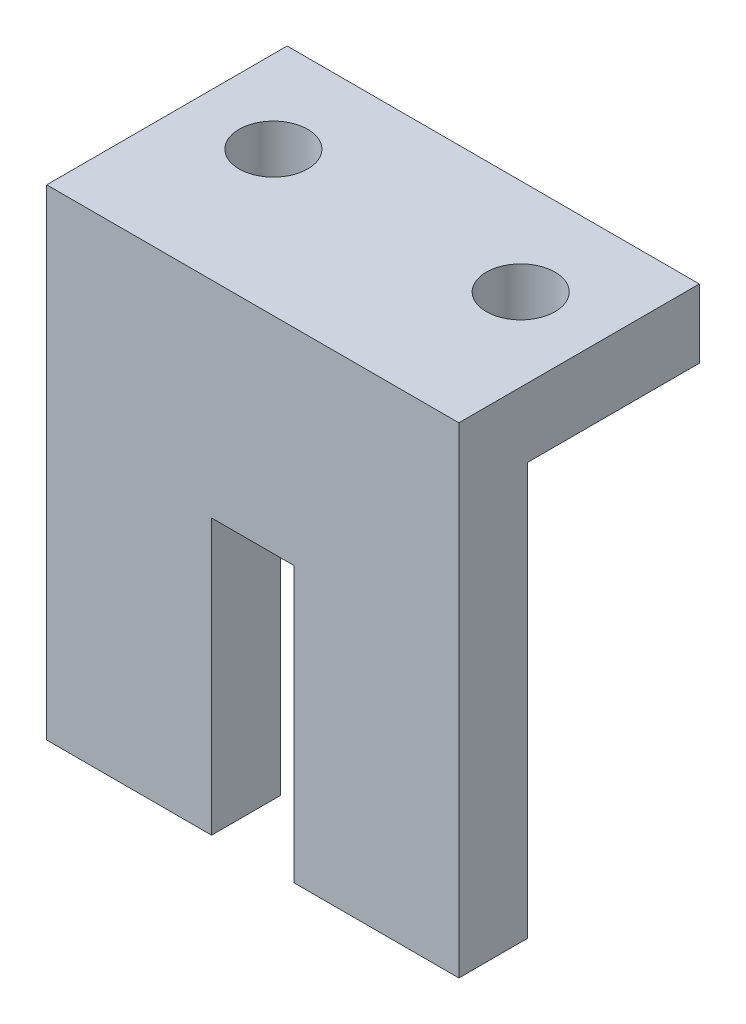
SolidWorks part; units mm, degrees
ref_plane "Front Plane" through (0, 0, 0) normal (0, 0, 1) x (1, 0, 0)
ref_plane "Top Plane" through (0, 0, 0) normal (0, 1, 0) x (1, 0, 0)
ref_plane "Right Plane" through (0, 0, 0) normal (1, 0, 0) x (0, 0, -1)
sketch "Sketch1" plane through (0, 0, 0) normal (0, 0, 1) x (1, 0, 0)
  line L0 (12, 0) -> (12, 20)
  line L1 (0, 0) -> (12, 0)
  line L2 (0, 0) -> (0, 30)
  line L4 (30, 0) -> (30, 30)
  line L5 (12, 20) -> (18, 20)
  line L6 (18, 20) -> (18, 0)
  line L7 (18, 0) -> (30, 0)
  line L8 (0, 30) -> (0, 35)
  line L9 (0, 35) -> (30, 35)
  line L10 (30, 35) -> (30, 30)
  dimension "D1" = 30
  dimension "D2" = 30
  dimension "D3" = 12
  dimension "D4" = 6
  dimension "D5" = 20
  dimension "D6" = 5
extrude "Boss-Extrude1" add sketch "Sketch1" along normal blind 5
sketch "Sketch2" plane through (0, 0, 0) normal (0, 0, -1) x (-1, 0, 0)
  line L0 (0, 35) -> (0, 0) construction
  line L1 (-30, 35) -> (0, 35)
  line L2 (-30, 35) -> (-30, 30)
  line L3 (-30, 30) -> (0, 30)
  line L4 (0, 35) -> (0, 30)
  dimension "D1" = 5
extrude "Boss-Extrude2" add sketch "Sketch2" along normal blind 19
sketch "Sketch3" plane through (0, 35, 0) normal (0, 1, 0) x (1, 0, 0)
  line L1 (30, -5) -> (30, 19) construction
  line L2 (0, -5) -> (30, -5)
  line L3 (0, -5) -> (0, 0)
  line L4 (0, 0) -> (30, 0)
  line L5 (30, -5) -> (30, 0)
  line L6 (0, -5) -> (0, 19) construction
  circle A0 centre (6, 5.5) radius 2.5
  circle A1 centre (24, 5.5) radius 2.5
  point P15 (0, 0)
  dimension "D2" = 5
  dimension "D3" = 5
  dimension "D5" = 6
  dimension "D6" = 5.5
  dimension "D7" = 5.5
  dimension "D1" = 5
  dimension "D4" = 6
extrude "Cut-Extrude1" cut sketch "Sketch3" against normal blind 19 contours A1 | A0
sketch "Sketch4" plane through (0, 35, 0) normal (0, 1, 0) x (1, 0, 0)
  line L0 (30, -5) -> (30, 19) construction
  line L1 (0, 19) -> (30, 19)
  line L2 (0, 19) -> (0, 12.5)
  line L3 (0, 12.5) -> (30, 12.5)
  line L4 (30, 19) -> (30, 12.5)
  circle A0 centre (6, 5.5) radius 2.5 construction
  dimension "D1" = 7
extrude "Cut-Extrude2" cut sketch "Sketch4" against normal through all
